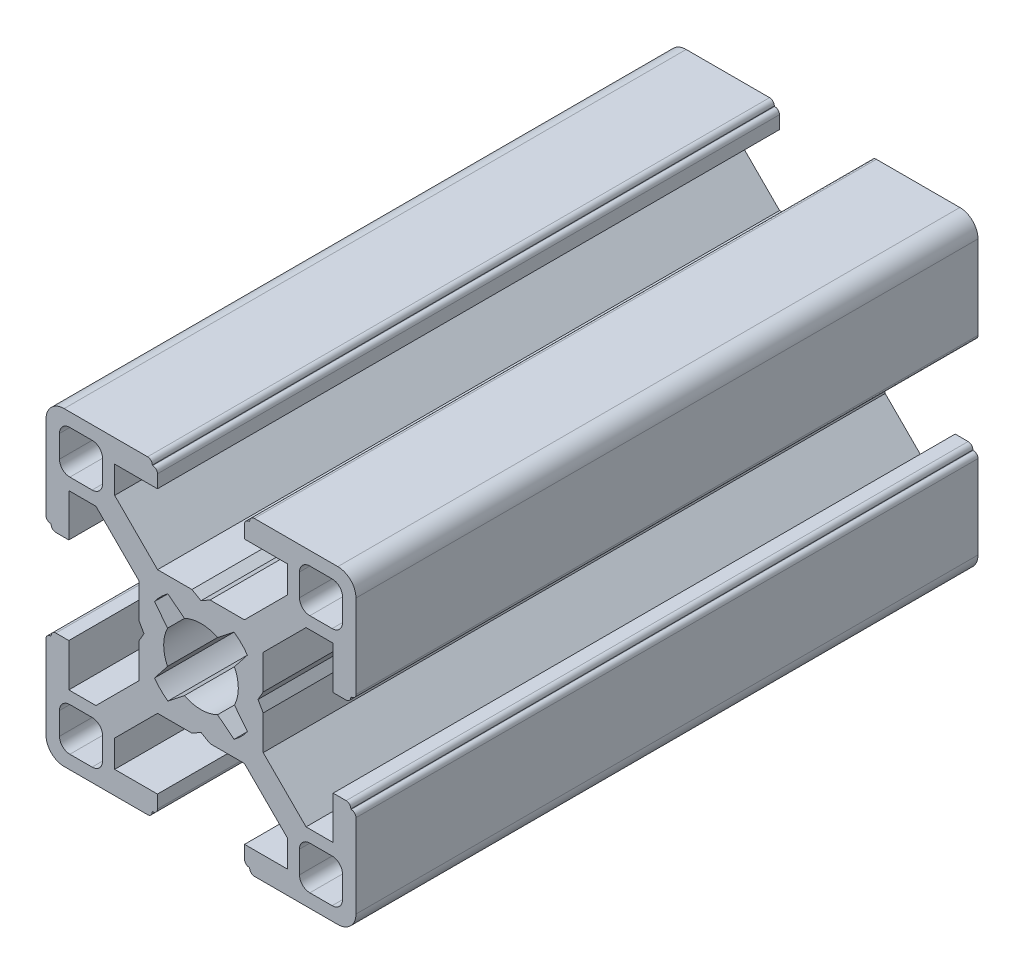
SolidWorks part; units mm, degrees
ref_plane "Front Plane" through (0, 0, 0) normal (0, 0, 1) x (1, 0, 0)
ref_plane "Top Plane" through (0, 0, 0) normal (0, 1, 0) x (1, 0, 0)
ref_plane "Right Plane" through (0, 0, 0) normal (1, 0, 0) x (0, 0, -1)
sketch "Sketch1" plane through (0, 0, 0) normal (0, 0, 1) x (1, 0, 0)
  line L0 (-8.325, 12.75) -> (-4.2, 12.75)
  line L1 (-4.2, 12.75) -> (-4.2, 14)
  line L2 (-4.65, 14.45) -> (-4.7, 14.45)
  line L3 (-4.7, 14.45) -> (-4.7, 14.5)
  line L4 (-5.15, 14.95) -> (-13.2, 14.95)
  line L5 (-14.95, 13.2) -> (-14.95, 5.15)
  line L6 (-14.5, 4.7) -> (-14.45, 4.7)
  line L7 (-14.45, 4.7) -> (-14.45, 4.65)
  line L8 (-14, 4.2) -> (-12.75, 4.2)
  line L9 (-12.75, 4.2) -> (-12.75, 8.325)
  line L10 (-12.75, 8.325) -> (-10.1352, 8.325)
  line L11 (-10.1352, 8.325) -> (-6, 4.1898)
  line L12 (-6, 4.1898) -> (-6, 0.875)
  line L13 (-6, 0.875) -> (-5.5, 0)
  line L14 (-5.5, 0) -> (-6, -0.875)
  line L15 (-6, -0.875) -> (-6, -4.1898)
  line L16 (-6, -4.1898) -> (-10.1352, -8.325)
  line L17 (-10.1352, -8.325) -> (-12.75, -8.325)
  line L18 (-12.75, -8.325) -> (-12.75, -4.2)
  line L19 (-12.75, -4.2) -> (-14, -4.2)
  line L20 (-14.45, -4.65) -> (-14.45, -4.7)
  line L21 (-14.45, -4.7) -> (-14.5, -4.7)
  line L22 (-14.95, -5.15) -> (-14.95, -13.2)
  line L23 (-13.2, -14.95) -> (-5.15, -14.95)
  line L24 (-4.7, -14.5) -> (-4.7, -14.45)
  line L25 (-4.7, -14.45) -> (-4.65, -14.45)
  line L26 (-4.2, -14) -> (-4.2, -12.75)
  line L27 (-4.2, -12.75) -> (-8.325, -12.75)
  line L28 (-8.325, -12.75) -> (-8.325, -10.1352)
  line L29 (-8.325, -10.1352) -> (-4.1898, -6)
  line L30 (-4.1898, -6) -> (-0.875, -6)
  line L31 (-0.875, -6) -> (0, -5.5)
  line L32 (0, -5.5) -> (0.875, -6)
  line L33 (0.875, -6) -> (4.1898, -6)
  line L34 (4.1898, -6) -> (8.325, -10.1352)
  line L35 (8.325, -10.1352) -> (8.325, -12.75)
  line L36 (8.325, -12.75) -> (4.2, -12.75)
  line L37 (4.2, -12.75) -> (4.2, -14)
  line L38 (4.65, -14.45) -> (4.7, -14.45)
  line L39 (4.7, -14.45) -> (4.7, -14.5)
  line L40 (5.15, -14.95) -> (13.2, -14.95)
  line L41 (14.95, -13.2) -> (14.95, -5.15)
  line L42 (14.5, -4.7) -> (14.45, -4.7)
  line L43 (14.45, -4.7) -> (14.45, -4.65)
  line L44 (14, -4.2) -> (12.75, -4.2)
  line L45 (12.75, -4.2) -> (12.75, -8.325)
  line L46 (12.75, -8.325) -> (10.1352, -8.325)
  line L47 (10.1352, -8.325) -> (6, -4.1898)
  line L48 (6, -4.1898) -> (6, -0.875)
  line L49 (6, -0.875) -> (5.5, 0)
  line L50 (5.5, 0) -> (6, 0.875)
  line L51 (6, 0.875) -> (6, 4.1898)
  line L52 (6, 4.1898) -> (10.1348, 8.3246)
  line L53 (10.1348, 8.3246) -> (12.75, 8.3246)
  line L54 (12.75, 8.3246) -> (12.75, 4.2)
  line L55 (12.75, 4.2) -> (14, 4.2)
  line L56 (14.45, 4.65) -> (14.45, 4.7)
  line L57 (14.45, 4.7) -> (14.5, 4.7)
  line L58 (14.95, 5.15) -> (14.95, 13.2)
  line L59 (13.2, 14.95) -> (5.15, 14.95)
  line L60 (4.7, 14.5) -> (4.7, 14.45)
  line L61 (4.7, 14.45) -> (4.65, 14.45)
  line L62 (4.2, 14) -> (4.2, 12.75)
  line L63 (4.2, 12.75) -> (8.3246, 12.75)
  line L64 (8.3246, 12.75) -> (8.3246, 10.1348)
  line L65 (8.3246, 10.1348) -> (4.1898, 6)
  line L66 (4.1898, 6) -> (0.875, 6)
  line L67 (0.875, 6) -> (0, 5.5)
  line L68 (0, 5.5) -> (-0.875, 6)
  line L69 (-0.875, 6) -> (-4.1898, 6)
  line L70 (-4.1898, 6) -> (-8.325, 10.1352)
  line L71 (-8.325, 10.1352) -> (-8.325, 12.75)
  line L72 (-4.4788, -3.1947) -> (-3.2263, -1.5971)
  line L73 (-3.2263, 1.5971) -> (-4.4788, 3.1947)
  line L74 (-3.1947, 4.4788) -> (-1.5971, 3.2263)
  line L75 (1.5971, 3.2263) -> (3.1947, 4.4788)
  line L76 (4.4788, 3.1947) -> (3.2263, 1.5971)
  line L77 (3.2263, -1.5971) -> (4.4788, -3.1947)
  line L78 (3.1947, -4.4788) -> (1.5971, -3.2263)
  line L79 (-1.5971, -3.2263) -> (-3.1947, -4.4788)
  line L80 (-13.65, -12.65) -> (-13.65, -10.5)
  line L81 (-12.65, -9.5) -> (-10.5, -9.5)
  line L82 (-9.5, -10.5) -> (-9.5, -12.65)
  line L83 (-10.5, -13.65) -> (-12.65, -13.65)
  line L84 (9.5, 10.5) -> (9.5, 12.65)
  line L85 (10.5, 13.65) -> (12.65, 13.65)
  line L86 (13.65, 12.65) -> (13.65, 10.5)
  line L87 (12.65, 9.5) -> (10.5, 9.5)
  line L88 (-13.65, 10.5) -> (-13.65, 12.65)
  line L89 (-12.65, 13.65) -> (-10.5, 13.65)
  line L90 (-9.5, 12.65) -> (-9.5, 10.5)
  line L91 (-10.5, 9.5) -> (-12.65, 9.5)
  line L92 (10.5, -9.5) -> (12.65, -9.5)
  line L93 (13.65, -10.5) -> (13.65, -12.65)
  line L94 (12.65, -13.65) -> (10.5, -13.65)
  line L95 (9.5, -12.65) -> (9.5, -10.5)
  arc A0 (-4.2, 14) -> (-4.65, 14.45) centre (-4.65, 14) ccw
  arc A1 (-4.7, 14.5) -> (-5.15, 14.95) centre (-5.15, 14.5) ccw
  arc A2 (-13.2, 14.95) -> (-14.95, 13.2) centre (-13.2, 13.2) ccw
  arc A3 (-14.95, 5.15) -> (-14.5, 4.7) centre (-14.5, 5.15) ccw
  arc A4 (-14.45, 4.65) -> (-14, 4.2) centre (-14, 4.65) ccw
  arc A5 (-14, -4.2) -> (-14.45, -4.65) centre (-14, -4.65) ccw
  arc A6 (-14.5, -4.7) -> (-14.95, -5.15) centre (-14.5, -5.15) ccw
  arc A7 (-14.95, -13.2) -> (-13.2, -14.95) centre (-13.2, -13.2) ccw
  arc A8 (-5.15, -14.95) -> (-4.7, -14.5) centre (-5.15, -14.5) ccw
  arc A9 (-4.65, -14.45) -> (-4.2, -14) centre (-4.65, -14) ccw
  arc A10 (4.2, -14) -> (4.65, -14.45) centre (4.65, -14) ccw
  arc A11 (4.7, -14.5) -> (5.15, -14.95) centre (5.15, -14.5) ccw
  arc A12 (13.2, -14.95) -> (14.95, -13.2) centre (13.2, -13.2) ccw
  arc A13 (14.95, -5.15) -> (14.5, -4.7) centre (14.5, -5.15) ccw
  arc A14 (14.45, -4.65) -> (14, -4.2) centre (14, -4.65) ccw
  arc A15 (14, 4.2) -> (14.45, 4.65) centre (14, 4.65) ccw
  arc A16 (14.5, 4.7) -> (14.95, 5.15) centre (14.5, 5.15) ccw
  arc A17 (14.95, 13.2) -> (13.2, 14.95) centre (13.2, 13.2) ccw
  arc A18 (5.15, 14.95) -> (4.7, 14.5) centre (5.15, 14.5) ccw
  arc A19 (4.65, 14.45) -> (4.2, 14) centre (4.65, 14) ccw
  arc A20 (-3.1947, -4.4788) -> (-4.4788, -3.1947) centre (0, 0) cw
  arc A21 (-3.2263, -1.5971) -> (-3.2263, 1.5971) centre (0, 0) cw
  arc A22 (-4.4788, 3.1947) -> (-3.1947, 4.4788) centre (0, 0) cw
  arc A23 (-1.5971, 3.2263) -> (1.5971, 3.2263) centre (0, 0) cw
  arc A24 (3.1947, 4.4788) -> (4.4788, 3.1947) centre (0, 0) cw
  arc A25 (3.2263, 1.5971) -> (3.2263, -1.5971) centre (0, 0) cw
  arc A26 (4.4788, -3.1947) -> (3.1947, -4.4788) centre (0, 0) cw
  arc A27 (1.5971, -3.2263) -> (-1.5971, -3.2263) centre (0, 0) cw
  arc A28 (-12.65, -13.65) -> (-13.65, -12.65) centre (-12.65, -12.65) cw
  arc A29 (-13.65, -10.5) -> (-12.65, -9.5) centre (-12.65, -10.5) cw
  arc A30 (-10.5, -9.5) -> (-9.5, -10.5) centre (-10.5, -10.5) cw
  arc A31 (-9.5, -12.65) -> (-10.5, -13.65) centre (-10.5, -12.65) cw
  arc A32 (10.5, 9.5) -> (9.5, 10.5) centre (10.5, 10.5) cw
  arc A33 (9.5, 12.65) -> (10.5, 13.65) centre (10.5, 12.65) cw
  arc A34 (12.65, 13.65) -> (13.65, 12.65) centre (12.65, 12.65) cw
  arc A35 (13.65, 10.5) -> (12.65, 9.5) centre (12.65, 10.5) cw
  arc A36 (-12.65, 9.5) -> (-13.65, 10.5) centre (-12.65, 10.5) cw
  arc A37 (-13.65, 12.65) -> (-12.65, 13.65) centre (-12.65, 12.65) cw
  arc A38 (-10.5, 13.65) -> (-9.5, 12.65) centre (-10.5, 12.65) cw
  arc A39 (-9.5, 10.5) -> (-10.5, 9.5) centre (-10.5, 10.5) cw
  arc A40 (9.5, -10.5) -> (10.5, -9.5) centre (10.5, -10.5) cw
  arc A41 (12.65, -9.5) -> (13.65, -10.5) centre (12.65, -10.5) cw
  arc A42 (13.65, -12.65) -> (12.65, -13.65) centre (12.65, -12.65) cw
  arc A43 (10.5, -13.65) -> (9.5, -12.65) centre (10.5, -12.65) cw
extrude "Boss-Extrude1" add sketch "Sketch1" against normal mid plane 60
